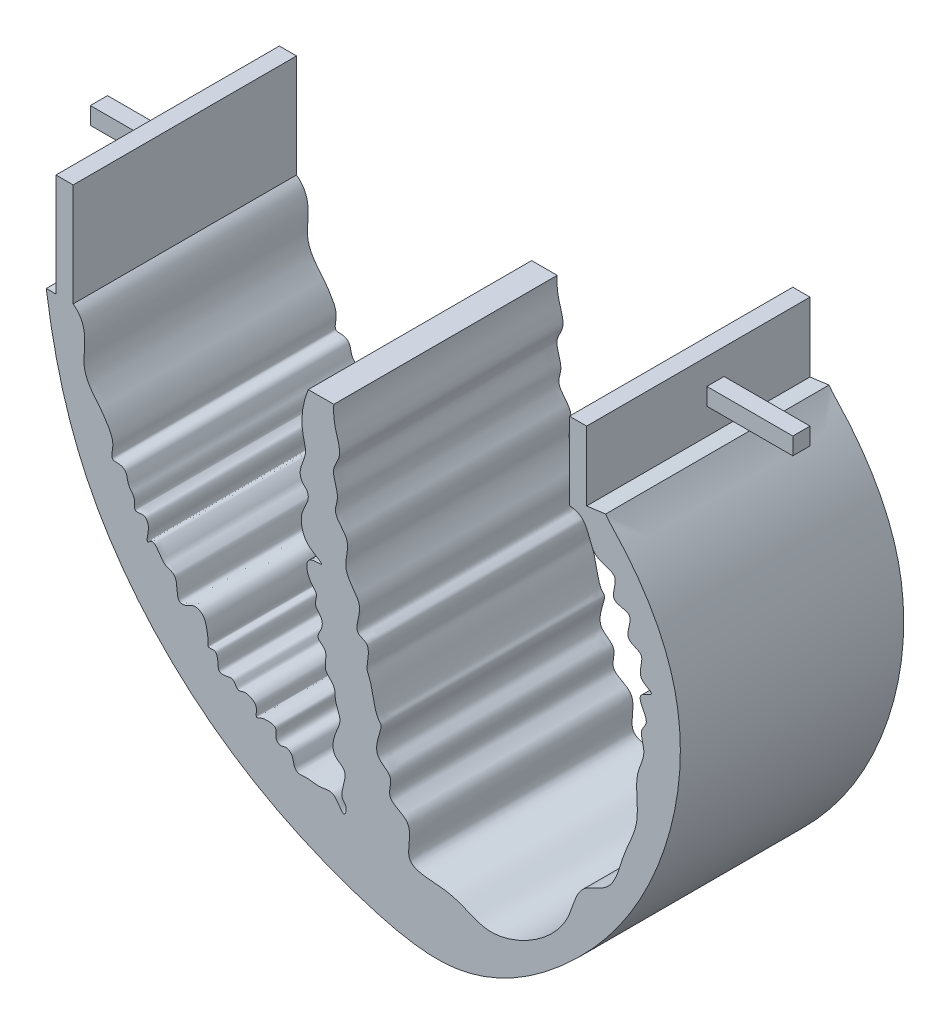
SolidWorks part; units mm, degrees
ref_plane "Front Plane" through (0, 0, 0) normal (0, 0, 1) x (1, 0, 0)
ref_plane "Top Plane" through (0, 0, 0) normal (0, 1, 0) x (1, 0, 0)
ref_plane "Right Plane" through (0, 0, 0) normal (1, 0, 0) x (0, 0, -1)
sketch "Sketch1" plane through (0, 0, 0) normal (0, 0, 1) x (1, 0, 0)
  line L0 (155.9186, 311.1659) -> (244.8186, 311.1659) construction
  line L1 (156.4284, 303.8008) -> (157.8631, 303.8008)
  line L2 (195.1505, 310.2179) -> (198.9304, 310.2179)
  line L3 (236.2948, 315.8866) -> (239.1049, 316.2649)
  line L6 (160.4031, 303.8008) -> (160.4031, 319.0408)
  line L7 (160.4031, 319.0408) -> (157.8631, 319.0408)
  line L8 (157.8631, 303.8008) -> (157.8631, 319.0408)
  line L10 (233.7548, 314.6833) -> (233.7548, 326.1133)
  line L11 (233.7548, 326.1133) -> (236.2948, 326.1133)
  line L12 (236.2948, 315.8866) -> (236.2948, 326.1133)
  spline S0 degree 3 poles (156.4284, 303.8008) (157.4149, 296.7275) (161.2888, 280.5085) (178.2163, 259.8183) (198.5453, 249.6184) (218.658, 245.0232) (234.9705, 255.6289) (248.3574, 273.7717) (252.562, 297.43) (244.0287, 311.0697) (239.4806, 315.7066) (239.1049, 316.2649) knots 0.117891 0.117891 0.117891 0.117891 0.184834 0.273022 0.359649 0.397817 0.461195 0.526427 0.612455 0.666069 0.672634 0.672634 0.672634 0.672634
  spline S8 degree 3 poles (160.4031, 303.8008) (162.2941, 302.3789) (162.1609, 299.7379) (161.9148, 296.3957) (162.8177, 294.2872) (164.4158, 292.5722) (165.7237, 290.6056) (166.5411, 288.8334) (165.7764, 286.5141) (167.4597, 286.8576) (168.4414, 286.0362) (168.3857, 284.5293) (169.7531, 283.6184) (169.2211, 281.4962) (170.9636, 282.2575) (171.5969, 281.0555) (171.5093, 280.2341) (171.1749, 278.4173) (172.1239, 279.5069) (172.9642, 278.5944) (173.3985, 277.8118) (174.2025, 277.0003) (175.4535, 276.8038) (175.8247, 275.2352) (175.7404, 273.3113) (177.3163, 273.5207) (178.1836, 274.304) (179.8106, 273.6975) (180.1589, 272.0142) (180.3885, 270.9092) (180.2673, 269.6248) (181.357, 270.1167) (181.7267, 269.2872) (181.8207, 268.5569) (181.8114, 267.2634) (183.0952, 267.4875) (184.2306, 267.7132) (184.6418, 266.2617) (185.6594, 266.8526) (186.6496, 266.6161) (187.7932, 265.9539) (187.2269, 264.1378) (188.3749, 264.8301) (189.1564, 264.8202) (190.728, 264.7412) (190.0775, 263.223) (191.0452, 262.4414) (191.9059, 262.9423) (193.0089, 262.1732) (192.9015, 261.0371) (193.6578, 260.2552) (195.1109, 260.559) (196.7712, 259.9512) (199.1827, 260.8909) (200.3998, 257.5847) (200.9385, 259.6247) (199.3455, 260.902) (201.6597, 263.9422) (198.3753, 265.3506) (198.9968, 268.1244) (200.2304, 270.3851) (198.9637, 272.2022) (199.2632, 274.319) (197.0238, 275.5519) (198.369, 278.0603) (196.1269, 279.12) (197.2468, 280.5144) (197.2952, 282.0718) (195.857, 283.0504) (196.6696, 284.7088) (195.0466, 285.888) (194.4409, 289.0637) (198.1906, 288.5422) (195.1715, 290.0128) (194.2609, 291.5812) (193.7484, 294.5389) (196.0084, 296.5906) (194.4389, 297.7146) knots 0 0 0 0 0.049996 0.065889 0.085586 0.106494 0.12633 0.14533 0.158777 0.169851 0.17682 0.189609 0.203968 0.215368 0.226544 0.234051 0.244077 0.254103 0.259848 0.2675 0.27863 0.285374 0.295913 0.307178 0.324488 0.33094 0.342393 0.353021 0.368289 0.381907 0.386446 0.3943 0.399826 0.405924 0.415167 0.425567 0.431874 0.44315 0.449762 0.456279 0.46939 0.478958 0.484911 0.493692 0.502959 0.5154 0.5222 0.52876 0.537962 0.549766 0.555958 0.562483 0.585296 0.601032 0.620439 0.629585 0.635431 0.669716 0.683063 0.711158 0.727063 0.746976 0.761152 0.77728 0.799704 0.811467 0.824176 0.835068 0.849297 0.860204 0.872607 0.897258 0.910614 0.929465 0.942875 0.963603 1 1 1 1
  spline S9 degree 3 poles (194.4389, 297.7146) (193.2395, 299.2283) (195.2731, 301.1728) (193.8381, 305.3352) (194.3382, 308.2132) (195.1505, 310.2179) knots 0 0 0 0 0.340369 0.485096 1 1 1 1
  spline S10 degree 3 poles (233.7548, 314.6833) (236.9481, 314.4817) (235.9348, 309.486) (241.6314, 309.6484) (239.2633, 305.3099) (243.8917, 305.6948) (241.3239, 301.6544) (245.5491, 301.1845) (243.1357, 297.7829) (246.8997, 296.6065) (242.7791, 295.7063) (245.9349, 293.0069) (243.9434, 291.0868) (245.3069, 288.5548) (243.0106, 284.7602) (244.5831, 279.3665) (241.4303, 274.0734) (240.4893, 268.2993) (234.8931, 267.0009) (234.1732, 262.628) (231.7495, 258.9002) (227.8379, 255.6353) (221.3672, 253.3017) (216.4272, 256.9185) (208.4548, 255.9598) (211.2737, 262.6018) (206.3604, 263.511) (208.0297, 267.0364) (204.1386, 268.3124) (206.6163, 273.0978) (205.2493, 272.8375) (204.2479, 278.5749) (203.5171, 278.0602) (204.5376, 282.674) (201.5301, 282.149) (203.0716, 285.8826) (201.9606, 287.9868) (199.9133, 290.06) (201.855, 293.9301) (198.617, 296.0822) (199.9781, 299.0373) (198.2252, 301.5284) (200.2974, 304.199) (199.0012, 307.0966) (198.8522, 309.174) (198.9304, 310.2179) knots 0 0 0 0 0.037446 0.059444 0.08019 0.0963 0.118583 0.133282 0.156259 0.168723 0.181203 0.205034 0.213726 0.232529 0.25537 0.302463 0.341301 0.386328 0.413156 0.448753 0.47034 0.508948 0.558767 0.60004 0.642673 0.674851 0.697745 0.715396 0.733762 0.762664 0.781599 0.792164 0.818097 0.837307 0.857123 0.872664 0.876318 0.893665 0.912488 0.929179 0.938318 0.956848 0.966872 0.984331 1 1 1 1
  dimension "D1" = 88.9
  dimension "D2" = 2.54
  dimension "D3" = 15.24
  dimension "D4" = 2.54
  dimension "D5" = 11.43
extrude "Boss-Extrude1" add sketch "Sketch1" along normal blind 33.02
sketch "Sketch2" plane through (157.8631, 0, 0) normal (-1, 0, 0) x (0, 0, 1)
  line L0 (33.02, 319.0408) -> (0, 319.0408) construction
  line L1 (12.7, 310.1508) -> (15.24, 310.1508)
  line L2 (12.7, 310.1508) -> (12.7, 312.6908)
  line L3 (12.7, 312.6908) -> (15.24, 312.6908)
  line L4 (15.24, 310.1508) -> (15.24, 312.6908)
  line L5 (33.02, 319.0408) -> (33.02, 303.8008) construction
  dimension "D1" = 2.54
  dimension "D2" = 2.54
  dimension "D3" = 6.35
  dimension "D4" = 17.78
extrude "Boss-Extrude2" add sketch "Sketch2" along normal blind 12.7
sketch "Sketch3" plane through (236.2948, 0, 0) normal (1, 0, 0) x (0, 0, -1)
  line L0 (-33.02, 326.1133) -> (0, 326.1133) construction
  line L1 (-15.24, 322.3033) -> (-12.7, 322.3033)
  line L2 (-15.24, 322.3033) -> (-15.24, 319.7633)
  line L3 (-15.24, 319.7633) -> (-12.7, 319.7633)
  line L4 (-12.7, 322.3033) -> (-12.7, 319.7633)
  line L5 (-33.02, 315.8866) -> (-33.02, 326.1133) construction
  dimension "D1" = 2.54
  dimension "D2" = 2.54
  dimension "D3" = 3.81
  dimension "D4" = 17.78
extrude "Boss-Extrude3" add sketch "Sketch3" along normal blind 12.7
